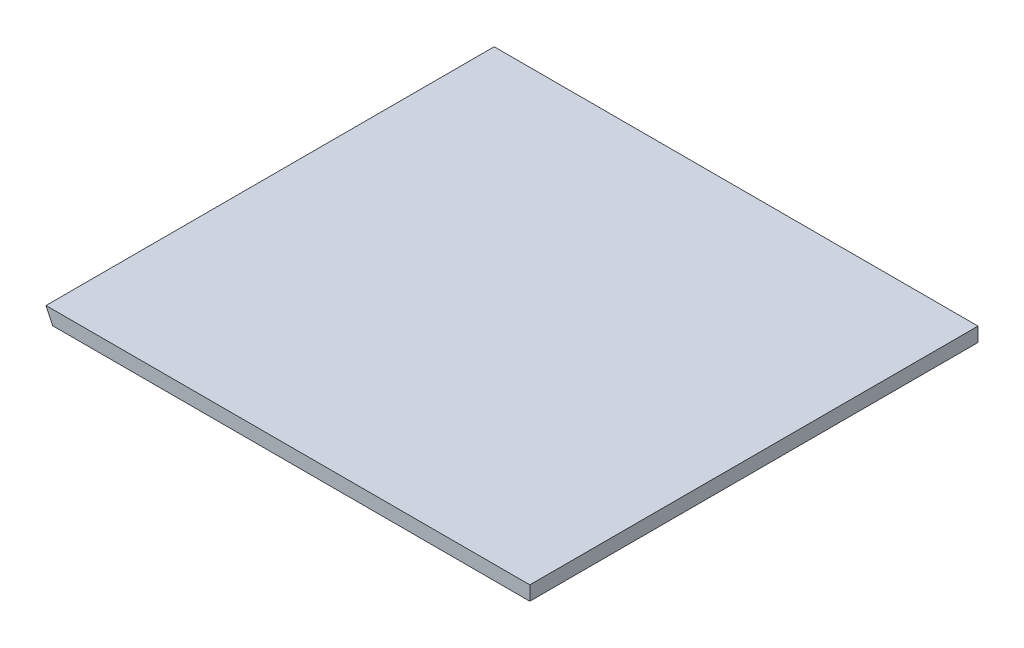
SolidWorks part; units mm, degrees
ref_plane "Front Plane" through (0, 0, 0) normal (0, 0, 1) x (1, 0, 0)
ref_plane "Top Plane" through (0, 0, 0) normal (0, 1, 0) x (1, 0, 0)
ref_plane "Right Plane" through (0, 0, 0) normal (1, 0, 0) x (0, 0, -1)
sketch "Sketch1" plane through (0, 0, 0) normal (0, 0, 1) x (1, 0, 0)
  line L0 (-438.5213, 22.225) -> (-536.0898, 228.9575) construction
  line L1 (-438.5213, 22.225) -> (-444.5151, 34.925)
  line L2 (-12.7, 327.025) -> (-12.7, 22.225) construction
  line L3 (-12.7, 34.925) -> (-12.7, 22.225)
  line L4 (-438.5213, 22.225) -> (-12.7, 22.225)
  line L5 (-12.7, 34.925) -> (-444.5151, 34.925)
  dimension "D1" = 12.7
extrude "Boss-Extrude1" add sketch "Sketch1" along normal up to surface (400 mm away)
